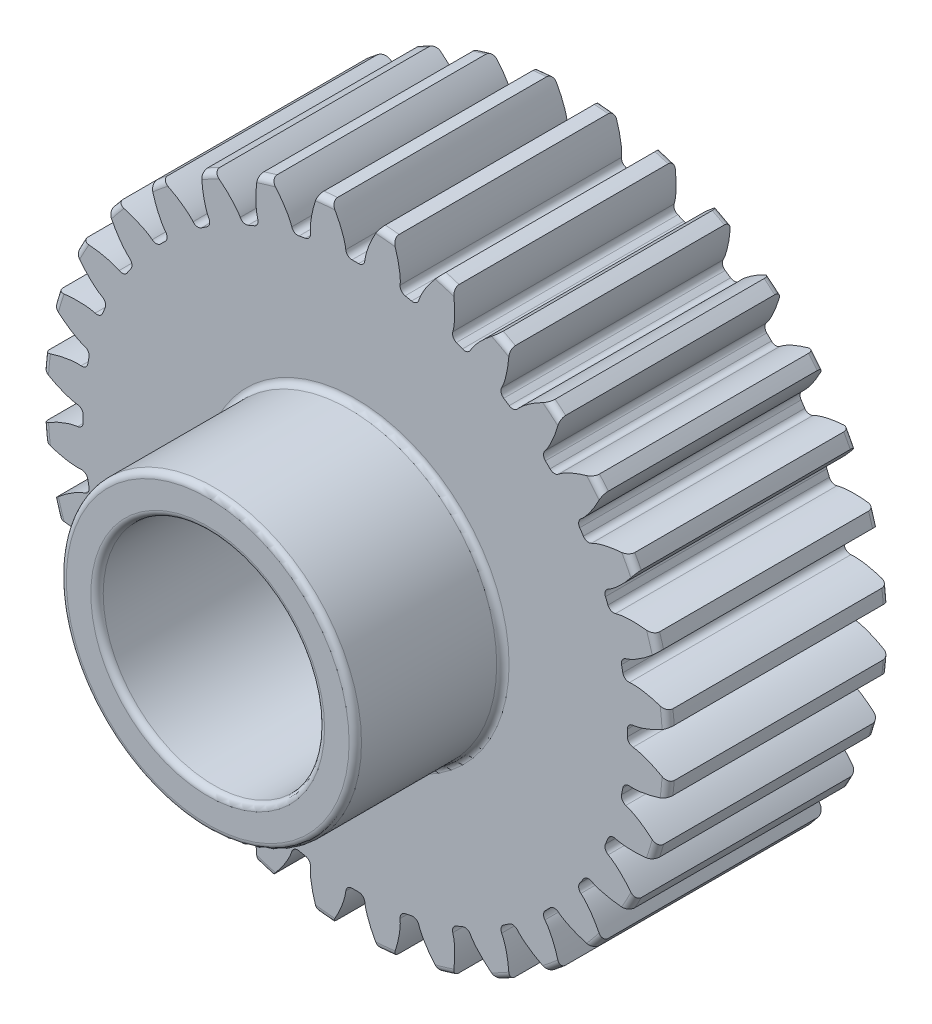
SolidWorks part; units mm, degrees
ref_plane "Front Plane" through (0, 0, 0) normal (0, 0, 1) x (1, 0, 0)
ref_plane "Top Plane" through (0, 0, 0) normal (0, 1, 0) x (1, 0, 0)
ref_plane "Right Plane" through (0, 0, 0) normal (1, 0, 0) x (0, 0, -1)
sketch "Sketch1" plane through (0, 0, 0) normal (0, 0, 1) x (1, 0, 0)
  line L0 (0, 0) -> (0, 25.4) construction
  line L1 (-8.1634, 28.3712) -> (8.1634, 22.4288) construction
  circle A0 centre (0, 0) radius 23.4156 construction
  circle A1 centre (0, 0) radius 26.9875 construction
  circle A2 centre (0, 0) radius 25.4 construction
  circle A3 centre (0, 0) radius 23.8682 construction
  circle A4 centre (0, 0) radius 9.525 construction
  circle A5 centre (0, 0) radius 21.59 construction
  point P8 (203.2, 0)
  point P13 (406.4, 0)
  dimension "OD | Outside Diameter" = 53.975
  dimension "Root Diameter" = 46.8312
  dimension "Gear Pitch Diameter" = 50.8
  dimension "Base Diameter" = 47.7364
  dimension "For Shaft Diameter" = 19.05
  dimension "Hub Diameter" = 43.18
  dimension "Pressure Angle" = 20
  dimension "Number of Teeth" = 812.8
  dimension "Gear Pitch | Diametral Pitch" = 406.4
sketch "Sketch2" plane through (0, 0, 0) normal (1, 0, 0) x (0, 0, -1)
  line L0 (-15.875, 0) -> (15.875, 0) construction
  line L1 (-15.875, 26.9875) -> (15.875, 26.9875) construction
  point P2 (0, 26.9875)
  point P4 (-3.175, 0)
  point P6 (-3.175, 26.9875)
  dimension "Overall Width" = 31.75
  dimension "Hub Width" = 12.7
  dimension "Face Width" = 19.05
sketch "Sketch3" plane through (0, 0, 0) normal (0, 0, 1) x (1, 0, 0)
  circle A0 centre (0, 0) radius 26.9875
  circle A1 centre (0, 0) radius 26.9875 construction
extrude "Boss-Extrude1" add sketch "Sketch3" against normal up to vertex (15.875 mm away) and the other way up to vertex (15.875 mm away) up to point (0, 0, -15.875) other way up to point (0, 0, 15.875)
sketch "Sketch5" plane through (0, 0, 0) normal (1, 0, 0) x (0, 0, -1)
  line L1 (-15.875, 26.9875) -> (-3.175, 26.9875)
  line L2 (-15.875, 26.9875) -> (-15.875, 21.59)
  line L3 (-15.875, 21.59) -> (-3.175, 21.59)
  line L4 (-3.175, 26.9875) -> (-3.175, 21.59)
  line L11 (15.875, 9.525) -> (-15.875, 9.525)
  line L12 (15.875, 9.525) -> (15.875, 0)
  line L13 (15.875, 0) -> (-15.875, 0)
  line L14 (-15.875, 9.525) -> (-15.875, 0)
  point P5 (0, 9.525)
  point P12 (0, 21.59)
revolve "Cut-Revolve1" cut sketch "Sketch5" angle 360 about L0
fillet "Fillet2" radius 0.5326 6 edges at (26.9875, 0, -15.875) (9.525, 0, -15.875) (9.525, 0, 15.875) (21.59, 0, 3.175) (26.9875, 0, 3.175) (21.59, 0, 15.875)
sketch "Sketch4" plane through (0, 0, 0) normal (0, 0, 1) x (1, 0, 0)
  line L0 (0, 0) -> (23.4019, 0.8003) construction
  line L2 (0, 0) -> (23.4019, -0.8003) construction
  line L4 (23.4019, 0.8003) -> (23.8542, 0.8157)
  line L5 (23.8542, -0.8157) -> (23.4019, -0.8003)
  arc A0 (23.4019, 0.8003) -> (23.4019, -0.8003) centre (0, 0) cw
  arc A3 (26.9089, 2.0577) -> (26.9089, -2.0577) centre (0, 0) cw
  circle A4 centre (0, 0) radius 26.9875 construction
  spline S0 degree 4 poles (23.8542, 0.8157) (23.8592, 0.816) (23.8729, 0.8167) (23.8989, 0.8189) (23.9413, 0.8234) (23.9952, 0.8305) (24.0647, 0.8414) (24.1465, 0.8562) (24.2362, 0.8746) (24.3337, 0.897) (24.4306, 0.9214) (24.5272, 0.9477) (24.6232, 0.9756) (24.7393, 1.0114) (24.8782, 1.0572) (25.04, 1.1149) (25.2228, 1.1851) (25.4085, 1.2619) (25.5905, 1.3418) (25.7737, 1.4274) (25.9504, 1.5136) (26.1331, 1.6083) (26.3013, 1.6982) (26.4888, 1.8044) (26.6399, 1.8918) (26.838, 2.0129) (26.9547, 2.0862) (27.0909, 2.1739) (27.1512, 2.214) (27.1883, 2.2386) knots 0 0 0 0 0 0.005377 0.015084 0.028532 0.04661 0.064855 0.092111 0.119476 0.146842 0.174209 0.201575 0.228941 0.256307 0.307035 0.361767 0.4165 0.471232 0.525964 0.580697 0.635429 0.690161 0.744894 0.799626 0.854358 0.909091 0.954545 1 1 1 1 1 construction
  spline S1 degree 4 poles (23.8542, 0.8157) (23.8592, 0.816) (23.8729, 0.8167) (23.8989, 0.8189) (23.9413, 0.8234) (23.9952, 0.8305) (24.0647, 0.8414) (24.1465, 0.8562) (24.2362, 0.8746) (24.3337, 0.897) (24.4306, 0.9214) (24.5272, 0.9477) (24.6232, 0.9756) (24.7393, 1.0114) (24.8782, 1.0572) (25.04, 1.1149) (25.2228, 1.1851) (25.4085, 1.2619) (25.5905, 1.3418) (25.7737, 1.4274) (25.9504, 1.5136) (26.1331, 1.6083) (26.3013, 1.6982) (26.4888, 1.8044) (26.6399, 1.8918) (26.7951, 1.9866) (26.8705, 2.0335) (26.9089, 2.0577) knots 0 0 0 0 0 0.005377 0.015084 0.028532 0.04661 0.064855 0.092111 0.119476 0.146842 0.174209 0.201575 0.228941 0.256307 0.307035 0.361767 0.4165 0.471232 0.525964 0.580697 0.635429 0.690161 0.744894 0.799626 0.854358 0.909091 0.909091 0.909091 0.909091 0.909091
  spline S2 degree 4 poles (23.8542, -0.8157) (23.8592, -0.816) (23.8729, -0.8167) (23.8989, -0.8189) (23.9413, -0.8234) (23.9952, -0.8305) (24.0647, -0.8414) (24.1465, -0.8562) (24.2362, -0.8746) (24.3337, -0.897) (24.4306, -0.9214) (24.5272, -0.9477) (24.6232, -0.9756) (24.7393, -1.0114) (24.8782, -1.0572) (25.04, -1.1149) (25.2228, -1.1851) (25.4085, -1.2619) (25.5905, -1.3418) (25.7737, -1.4274) (25.9504, -1.5136) (26.1331, -1.6083) (26.3013, -1.6982) (26.4888, -1.8044) (26.6399, -1.8918) (26.838, -2.0129) (26.9547, -2.0862) (27.0909, -2.1739) (27.1512, -2.214) (27.1883, -2.2386) knots 0 0 0 0 0 0.005377 0.015084 0.028532 0.04661 0.064855 0.092111 0.119476 0.146842 0.174209 0.201575 0.228941 0.256307 0.307035 0.361767 0.4165 0.471232 0.525964 0.580697 0.635429 0.690161 0.744894 0.799626 0.854358 0.909091 0.954545 1 1 1 1 1 construction
  spline S3 degree 4 poles (23.8542, -0.8157) (23.8592, -0.816) (23.8729, -0.8167) (23.8989, -0.8189) (23.9413, -0.8234) (23.9952, -0.8305) (24.0647, -0.8414) (24.1465, -0.8562) (24.2362, -0.8746) (24.3337, -0.897) (24.4306, -0.9214) (24.5272, -0.9477) (24.6232, -0.9756) (24.7393, -1.0114) (24.8782, -1.0572) (25.04, -1.1149) (25.2228, -1.1851) (25.4085, -1.2619) (25.5905, -1.3418) (25.7737, -1.4274) (25.9504, -1.5136) (26.1331, -1.6083) (26.3013, -1.6982) (26.4888, -1.8044) (26.6399, -1.8918) (26.7951, -1.9866) (26.8705, -2.0335) (26.9089, -2.0577) knots 0 0 0 0 0 0.005377 0.015084 0.028532 0.04661 0.064855 0.092111 0.119476 0.146842 0.174209 0.201575 0.228941 0.256307 0.307035 0.361767 0.4165 0.471232 0.525964 0.580697 0.635429 0.690161 0.744894 0.799626 0.854358 0.909091 0.909091 0.909091 0.909091 0.909091
  dimension "D1" = 46.8312
extrude "Cut-Extrude1" cut sketch "Sketch4" against normal through all both and the other way through all
fillet "Fillet1" radius 0.5326 2 edges at (23.4019, -0.8003, -6.35) (23.4019, 0.8003, -6.35)
pattern_circular "CirPattern1" count 32 over 360 about axis through (0, 0, 15.875) along (0, 0, -1) of "Cut-Extrude1", "Fillet1"
sketch "Sketch6" plane through (0, 0, 15.875) normal (0, 0, 1) x (1, 0, 0)
  circle A0 centre (0, 0) radius 12.7
  circle A1 centre (0, 0) radius 22.1226
  point P4 (0, 0)
  dimension "D1" = 25.4
extrude "Cut-Extrude2" cut sketch "Sketch6" against normal up to surface (12.7 mm away) up to face at (0, 0, 3.175)
fillet "Fillet3" radius 0.5334 2 edges at (12.7, 0, 3.175) (12.7, 0, 15.875)
sketch "Sketch8" plane through (0, 0, 3.175) normal (0, 0, 1) x (1, 0, 0)
  circle A0 centre (0, 0) radius 25.4
  point P4 (0, 0)
  dimension "D1" = 50.8
equation "\"Root Diameter@Sketch1\"=\"Root Diameter\""
equation "\"OD | Outside Diameter@Sketch1\"=\"Outside Diameter\""
equation "\"D1@CirPattern1\"=\"Number of Teeth\""
equation "\"Diametral Pitch\"= 16"
equation "\"Number of Teeth\"= 32"
equation "\"Pressure Angle\"=20"
equation "\"Pitch Diameter\"= \"Number of Teeth\" / \"Diametral Pitch\""
equation "\"Base Diameter\"= \"Pitch Diameter\" * cos ( \"Pressure Angle\" )"
equation "\"Outside Diameter\"= ( \"Number of Teeth\" + 2 ) / \"Diametral Pitch\""
equation "\"Dedendum\"= 1.25 / \"Diametral Pitch\""
equation "\"Root Diameter\"= \"Pitch Diameter\" - ( 2 * \"Dedendum\" )"
equation "\"Pitch Angle\"= 360deg / \"Number of Teeth\""
equation "\"Alpha\"= sqr ( \"Pitch Diameter\" ^ 2 - \"Base Diameter\" ^ 2 ) / \"Base Diameter\" * 180 / PI - \"Pressure Angle\""
equation "\"Beta\"= ( \"Pitch Angle\" / 4 - \"Alpha\" )"
equation "\"Phi\"= sqr ( ( \"Outside Diameter\" / 2 ) ^ 2 - ( \"Base Diameter\" / 2 ) ^ 2 ) / ( \"Base Diameter\" / 2 )"
equation "\"Addendum\"= 1 / \"Diametral Pitch\""
equation "\"WorkingDepth\"= 2 / \"Diametral Pitch\""
equation "\"WholeDepth\"= 2.25 / \"Diametral Pitch\""
equation "\"Clearance\"= 0.25 / \"Diametral Pitch\""
equation "\"ToothThickness\"= ( pi * 2 ) / \"Diametral Pitch\""
equation "\"CircularPitch\"= pi / \"Diametral Pitch\""
equation "\"Number of Teeth@Sketch1\"=\"Number of Teeth\""
equation "\"Gear Pitch | Diametral Pitch@Sketch1\"=\"Diametral Pitch\""
equation "\"Pressure Angle@Sketch1\"=\"Pressure Angle\""
equation "\"Gear Pitch Diameter@Sketch1\"=\"Pitch Diameter\""
equation "\"Base Diameter@Sketch1\"=\"Base Diameter\""
equation "\"Fillet\"= \"Clearance\" * cos ( \"Pressure Angle\" ) * tan ( ( 90 + \"Pressure Angle\" ) / 2 )"
equation "\"D1@Fillet1\"=\"Fillet\""
equation "\"D1@Sketch4\"=if( \"Base Diameter\">\"Root Diameter\",\"Root Diameter\",\"Base Diameter\"-.00001)"
equation "\"D1@Fillet2\"=\"Fillet\""
